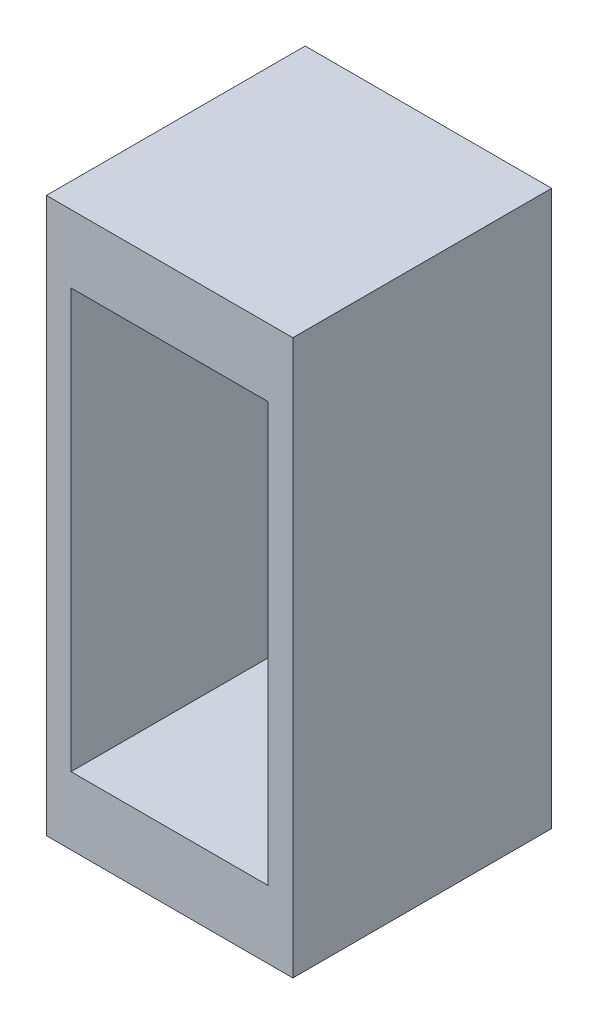
SolidWorks part; units mm, degrees
ref_plane "Front Plane" through (0, 0, 0) normal (0, 0, 1) x (1, 0, 0)
ref_plane "Top Plane" through (0, 0, 0) normal (0, 1, 0) x (1, 0, 0)
ref_plane "Right Plane" through (0, 0, 0) normal (1, 0, 0) x (0, 0, -1)
sketch "Sketch2" plane through (0, 0, 0) normal (0, 0, 1) x (1, 0, 0)
  line L1 (-10.16, -21.59) -> (10.16, -21.59)
  line L2 (-10.16, -21.59) -> (-10.16, 21.59)
  line L3 (-10.16, 21.59) -> (10.16, 21.59)
  line L4 (10.16, -21.59) -> (10.16, 21.59)
  line L5 (-10.16, -21.59) -> (10.16, 21.59) construction
  line L6 (-10.16, 21.59) -> (10.16, -21.59) construction
  line L7 (12.7, -28.575) -> (-12.7, -28.575)
  line L8 (12.7, -28.575) -> (12.7, 28.575)
  line L9 (12.7, 28.575) -> (-12.7, 28.575)
  line L10 (-12.7, -28.575) -> (-12.7, 28.575)
  line L11 (12.7, -28.575) -> (-12.7, 28.575) construction
  line L12 (12.7, 28.575) -> (-12.7, -28.575) construction
  point P0 (0, 0)
  point P6 (0, 0)
  dimension "D1" = 20.32
  dimension "D2" = 25.4
  dimension "D3" = 43.18
  dimension "D4" = 57.15
extrude "Boss-Extrude2" add sketch "Sketch2" along normal blind 26.67
sketch "Sketch3" plane through (0, -28.575, 0) normal (0, -1, 0) x (1, 0, 0)
  line L0 (-12.7, 0) -> (12.7, 0) construction
  line L1 (-6.35, -6.6496) -> (6.35, -6.6496)
  line L2 (-6.35, -6.6496) -> (-6.35, 6.0504)
  line L3 (-6.35, 6.0504) -> (6.35, 6.0504)
  line L4 (6.35, -6.6496) -> (6.35, 6.0504)
  line L5 (-6.35, -6.6496) -> (6.35, 6.0504) construction
  line L6 (-6.35, 6.0504) -> (6.35, -6.6496) construction
  point P0 (0, -0.2996)
  point P7 (0, 0)
  dimension "D1" = 12.7
  dimension "D2" = 12.7
  dimension "D3" = 0
extrude "Cut-Extrude1" cut sketch "Sketch3" against normal up to next
